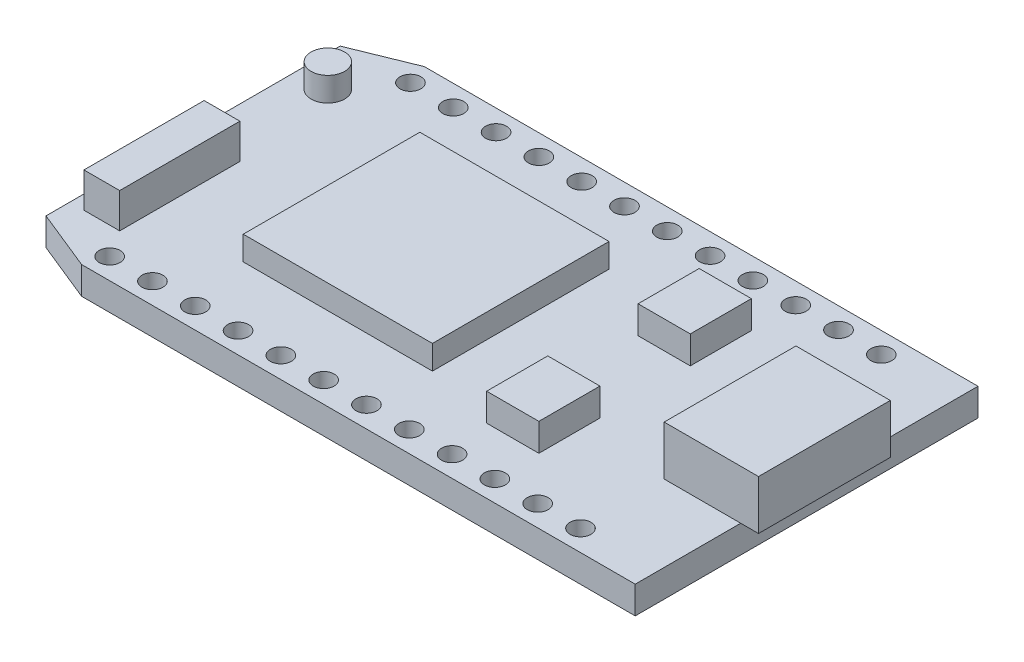
SolidWorks part; units mm, degrees
ref_plane "Front Plane" through (0, 0, 0) normal (0, 0, 1) x (1, 0, 0)
ref_plane "Top Plane" through (0, 0, 0) normal (0, 1, 0) x (1, 0, 0)
ref_plane "Right Plane" through (0, 0, 0) normal (1, 0, 0) x (0, 0, -1)
sketch "Sketch1" plane through (0, 0, 0) normal (0, 1, 0) x (1, 0, 0)
  line L1 (-18.275, -10.21) -> (18.275, -10.21)
  line L2 (-18.275, -10.21) -> (-18.275, 10.21)
  line L3 (-18.275, 10.21) -> (18.275, 10.21)
  line L4 (18.275, -10.21) -> (18.275, 10.21)
  line L5 (-18.275, -10.21) -> (18.275, 10.21) construction
  line L6 (-18.275, 10.21) -> (18.275, -10.21) construction
  point P0 (0, 0)
  dimension "D1" = 20.42
  dimension "D2" = 36.55
extrude "Boss-Extrude1" add sketch "Sketch1" along normal blind 1.64
chamfer "Chamfer1" distance 1.45 distance2 3.57 1 edges at (-18.275, 0.82, 10.21)
chamfer "Chamfer2" distance 3.57 distance2 1.45 1 edges at (-18.275, 0.82, -10.21)
sketch "Sketch3" plane through (0, 1.64, 0) normal (0, 1, 0) x (1, 0, 0)
  line L0 (0, 0) -> (50000, 0) construction
  line L1 (13.715, 3.925) -> (19.335, 3.925)
  line L2 (13.715, 3.925) -> (13.715, -3.925)
  line L3 (13.715, -3.925) -> (19.335, -3.925)
  line L4 (19.335, 3.925) -> (19.335, -3.925)
  line L5 (13.715, 3.925) -> (19.335, -3.925) construction
  line L6 (13.715, -3.925) -> (19.335, 3.925) construction
  line L7 (18.275, -10.21) -> (18.275, 10.21) construction
  point P0 (16.525, 0)
  dimension "D1" = 7.85
  dimension "D2" = 5.62
  dimension "D3" = 1.06
extrude "Boss-Extrude2" add sketch "Sketch3" along normal blind 2.94
sketch "Sketch4" plane through (0, 1.64, 0) normal (0, 1, 0) x (1, 0, 0)
  line L0 (18.275, 3.925) -> (18.275, 10.21) construction
  line L1 (5.545, 2.69) -> (8.655, 2.69)
  line L2 (5.545, 2.69) -> (5.545, 6.33)
  line L3 (5.545, 6.33) -> (8.655, 6.33)
  line L4 (8.655, 2.69) -> (8.655, 6.33)
  line L5 (5.545, 2.69) -> (8.655, 6.33) construction
  line L6 (5.545, 6.33) -> (8.655, 2.69) construction
  line L11 (-14.705, -10.21) -> (18.275, -10.21) construction
  line L12 (0, 0) -> (50000, 0) construction
  line L13 (5.545, -6.33) -> (8.655, -6.33)
  line L14 (8.655, -2.69) -> (8.655, -6.33)
  line L15 (5.545, -2.69) -> (8.655, -2.69)
  line L16 (5.545, -2.69) -> (5.545, -6.33)
  point P0 (7.1, 4.51)
  dimension "D1" = 3.64
  dimension "D2" = 3.11
  dimension "D3" = 12.73
  dimension "D4" = 16.54
extrude "Boss-Extrude3" add sketch "Sketch4" along normal blind 1.65
sketch "Sketch5" plane through (0, 1.64, 0) normal (0, 1, 0) x (1, 0, 0)
  line L0 (18.275, 10.21) -> (-14.705, 10.21) construction
  line L1 (-17.435, -7.34) -> (-15.305, -7.34)
  line L2 (-17.435, -7.34) -> (-17.435, -0.18)
  line L3 (-17.435, -0.18) -> (-15.305, -0.18)
  line L4 (-15.305, -7.34) -> (-15.305, -0.18)
  line L5 (-17.435, -7.34) -> (-15.305, -0.18) construction
  line L6 (-17.435, -0.18) -> (-15.305, -7.34) construction
  line L7 (18.275, -10.21) -> (18.275, -3.925) construction
  point P0 (-16.37, -3.76)
  dimension "D1" = 7.16
  dimension "D2" = 2.13
  dimension "D3" = 17.55
  dimension "D4" = 35.71
extrude "Boss-Extrude4" add sketch "Sketch5" along normal blind 2.08
sketch "Sketch6" plane through (0, 1.64, 0) normal (0, 1, 0) x (1, 0, 0)
  line L0 (0, 0) -> (-50000, 0) construction
  line L1 (-10.025, -5.26) -> (1.245, -5.26)
  line L2 (-10.025, -5.26) -> (-10.025, 5.26)
  line L3 (-10.025, 5.26) -> (1.245, 5.26)
  line L4 (1.245, -5.26) -> (1.245, 5.26)
  line L5 (-10.025, -5.26) -> (1.245, 5.26) construction
  line L6 (-10.025, 5.26) -> (1.245, -5.26) construction
  line L7 (-18.275, 8.76) -> (-18.275, -8.76) construction
  point P0 (-4.39, 0)
  dimension "D1" = 11.27
  dimension "D2" = 10.52
  dimension "D3" = 19.52
extrude "Boss-Extrude5" add sketch "Sketch6" along normal blind 1.43
sketch "Sketch7" plane through (0, 1.64, 0) normal (0, 1, 0) x (1, 0, 0)
  line L0 (-18.275, 8.76) -> (-18.275, -8.76) construction
  line L1 (18.275, 10.21) -> (-14.705, 10.21) construction
  circle A0 centre (-16.405, 6.16) radius 1
  dimension "D1" = 2
  dimension "D2" = 1.87
  dimension "D3" = 4.05
extrude "Boss-Extrude6" add sketch "Sketch7" along normal blind 1.43
sketch "Sketch8" plane through (0, 1.64, 0) normal (0, 1, 0) x (1, 0, 0)
  line L0 (-14.705, -10.21) -> (18.275, -10.21) construction
  line L1 (18.275, -10.21) -> (18.275, -3.925) construction
  line L2 (0, 0) -> (50000, 0) construction
  circle A0 centre (13.765, -8.96) radius 0.625
  circle A1 centre (11.215, -8.96) radius 0.625
  circle A2 centre (8.665, -8.96) radius 0.625
  circle A3 centre (6.115, -8.96) radius 0.625
  circle A4 centre (3.565, -8.96) radius 0.625
  circle A5 centre (1.015, -8.96) radius 0.625
  circle A6 centre (-1.535, -8.96) radius 0.625
  circle A7 centre (-4.085, -8.96) radius 0.625
  circle A8 centre (-6.635, -8.96) radius 0.625
  circle A9 centre (-9.185, -8.96) radius 0.625
  circle A10 centre (-11.735, -8.96) radius 0.625
  circle A11 centre (-14.285, -8.96) radius 0.625
  circle A12 centre (-14.285, 8.96) radius 0.625
  circle A13 centre (-11.735, 8.96) radius 0.625
  circle A14 centre (-9.185, 8.96) radius 0.625
  circle A15 centre (3.565, 8.96) radius 0.625
  circle A16 centre (-6.635, 8.96) radius 0.625
  circle A17 centre (-4.085, 8.96) radius 0.625
  circle A18 centre (-1.535, 8.96) radius 0.625
  circle A19 centre (1.015, 8.96) radius 0.625
  circle A20 centre (6.115, 8.96) radius 0.625
  circle A21 centre (8.665, 8.96) radius 0.625
  circle A22 centre (11.215, 8.96) radius 0.625
  circle A23 centre (13.765, 8.96) radius 0.625
  dimension "D1" = 1.25
  dimension "D2" = 1.25
  dimension "D3" = 4.51
  dimension "D4" = 12
extrude "Cut-Extrude1" cut sketch "Sketch8" against normal through all
